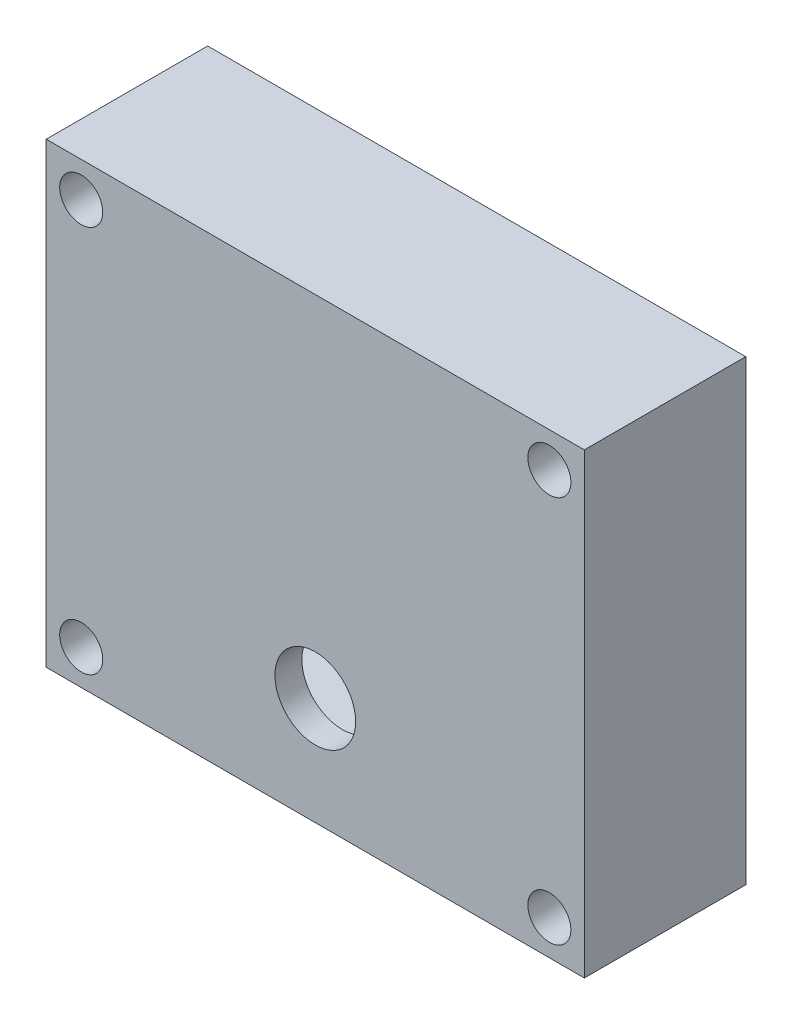
SolidWorks part; units mm, degrees
ref_plane "Front Plane" through (0, 0, 0) normal (0, 0, 1) x (1, 0, 0)
ref_plane "Top Plane" through (0, 0, 0) normal (0, 1, 0) x (1, 0, 0)
ref_plane "Right Plane" through (0, 0, 0) normal (1, 0, 0) x (0, 0, -1)
sketch "Sketch1" plane through (0, 0, 0) normal (0, 0, 1) x (1, 0, 0)
  line L1 (-50, 42.5) -> (50, 42.5)
  line L2 (-50, 42.5) -> (-50, -42.5)
  line L3 (-50, -42.5) -> (50, -42.5)
  line L4 (50, 42.5) -> (50, -42.5)
  line L5 (-50, 42.5) -> (50, -42.5) construction
  line L6 (-50, -42.5) -> (50, 42.5) construction
  point P0 (0, 0)
  dimension "D1" = 85
  dimension "D2" = 100
extrude "Boss-Extrude1" add sketch "Sketch1" along normal blind 30
sketch "Sketch3" plane through (0, 0, 30) normal (0, 0, 1) x (1, 0, 0)
  line L0 (-50, 42.5) -> (-50, -42.5) construction
  line L1 (50, 42.5) -> (-50, 42.5) construction
  line L2 (50, -42.5) -> (50, 42.5) construction
  line L3 (-11.6698, 0) -> (23.8522, 0) construction
  circle A0 centre (-43.5, 36) radius 2.5
  circle A1 centre (43.5, 36) radius 2.5
  circle A2 centre (43.5, -36) radius 2.5
  circle A3 centre (-43.5, -36) radius 2.5
  dimension "D1" = 6.5
  dimension "5" = 5
  dimension "D2" = 6.5
  dimension "D3" = 6.5
extrude "Cut-Extrude1" cut sketch "Sketch3" against normal blind 50
sketch "Sketch4" plane through (0, 0, 30) normal (0, 0, 1) x (1, 0, 0)
  circle A0 centre (-43.5, 36) radius 4
  circle A1 centre (43.5, 36) radius 4
  circle A2 centre (-43.5, -36) radius 4
  circle A3 centre (43.5, -36) radius 4
  dimension "D1" = 8
extrude "Cut-Extrude2" cut sketch "Sketch4" against normal blind 20
sketch "Sketch7" plane through (0, 0, 0) normal (0, 0, -1) x (-1, 0, 0)
  line L1 (-32, 37) -> (32, 37)
  line L2 (-42, 27) -> (-42, -27)
  line L3 (-32, -37) -> (32, -37)
  line L4 (42, 27) -> (42, -27)
  line L5 (-42, 37) -> (42, -37) construction
  line L6 (-42, -37) -> (42, 37) construction
  arc A0 (-42, -27) -> (-32, -37) centre (-32, -27) ccw
  arc A1 (32, -37) -> (42, -27) centre (32, -27) ccw
  arc A2 (32, 37) -> (42, 27) centre (32, 27) cw
  arc A3 (-32, 37) -> (-42, 27) centre (-32, 27) ccw
  point P0 (0, 0)
  dimension "D3" = 10
  dimension "D1" = 74
  dimension "D2" = 84
extrude "Cut-Extrude5" cut sketch "Sketch7" against normal blind 25
sketch "Sketch8" plane through (0, 0, 30) normal (0, 0, 1) x (1, 0, 0)
  line L0 (0, 42.5) -> (0, -42.5) construction
  line L1 (50, 42.5) -> (-50, 42.5) construction
  line L2 (-50, -42.5) -> (50, -42.5) construction
  circle A0 centre (0, -22.5) radius 7.5
  dimension "D1" = 15
  dimension "D2" = 20
extrude "Cut-Extrude6" cut sketch "Sketch8" against normal through all
